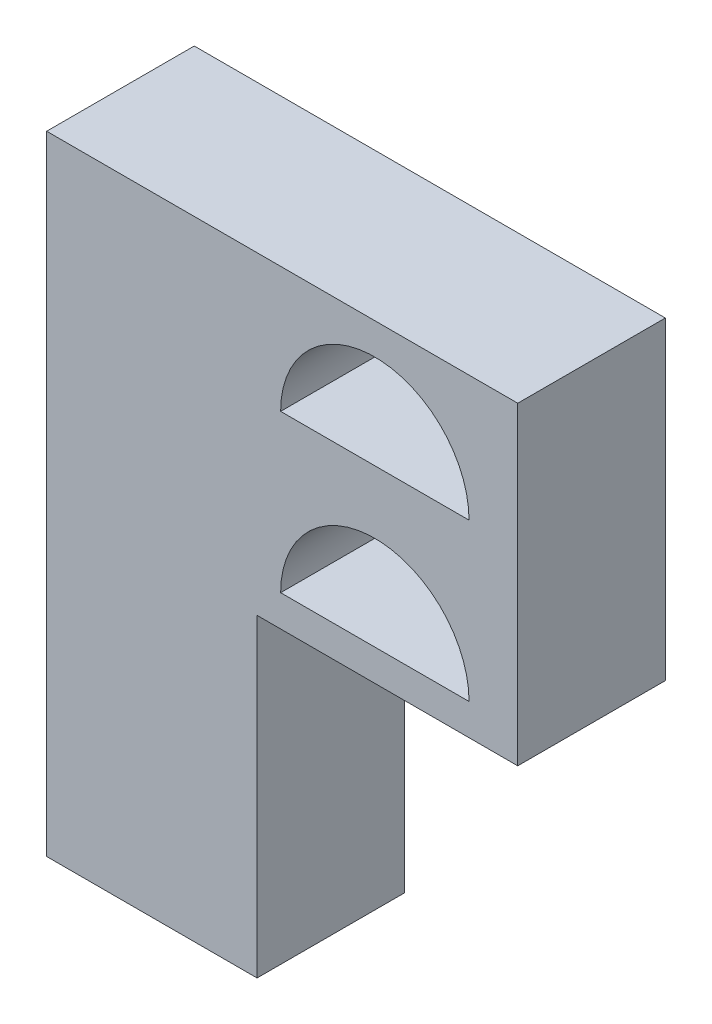
SolidWorks part; units mm, degrees
ref_plane "Front Plane" through (0, 0, 0) normal (0, 0, 1) x (1, 0, 0)
ref_plane "Top Plane" through (0, 0, 0) normal (0, 1, 0) x (1, 0, 0)
ref_plane "Right Plane" through (0, 0, 0) normal (1, 0, 0) x (0, 0, -1)
sketch "Sketch3" plane through (0, 0, 0) normal (0, 0, 1) x (1, 0, 0)
  line L0 (4.1, 15) -> (4.1, 0) construction
  line L2 (-3.35, 5) -> (-3.35, -5)
  line L3 (-3.35, -5) -> (3.35, -5)
  line L4 (3.35, 5) -> (3.35, -5)
  line L5 (-3.35, 5) -> (3.35, -5) construction
  line L6 (-3.35, -5) -> (3.35, 5) construction
  line L7 (3.35, 5) -> (6.63, 5)
  line L8 (-3.35, 5) -> (-3.35, 15)
  line L9 (-3.35, 15) -> (10.65, 15)
  line L11 (10.65, 10) -> (-3.35, 10) construction
  line L12 (10.1, 11) -> (4.1, 11) construction
  line L13 (6.63, 5) -> (3.35, 5)
  line L17 (6.63, 5) -> (10.65, 5)
  line L20 (10.1, 11) -> (4.1, 11)
  line L21 (10.65, 15) -> (11.65, 15)
  line L23 (10.1, 6) -> (4.1, 6)
  line L25 (10.65, 5) -> (11.65, 5)
  line L26 (11.65, 15) -> (11.65, 5)
  arc A1 (10.1, 11) -> (4.1, 11) centre (7.1, 11) ccw
  arc A2 (10.1, 6) -> (4.1, 6) centre (7.1, 6) ccw
  point P0 (0, 0)
  dimension "D1" = 6.7
  dimension "D2" = 10
  dimension "D3" = 1.5
  dimension "D4" = 1
  dimension "D5" = 14
  dimension "D6" = 1
  dimension "D7" = 2
  dimension "D8" = 6
extrude "Boss-Extrude2" add sketch "Sketch3" along normal blind 4.7
sketch "Sketch4" plane through (-3.35, 0, 0) normal (-1, 0, 0) x (0, 0, 1)
  line L0 (0, 5) -> (4.7, 5) construction
  line L1 (4.7, 15) -> (0, 15) construction
  line L6 (0, 10.0972) -> (4.7, 10.0972) construction
  line L10 (0, 12.5972) -> (4.7, 12.5972) construction
  line L11 (0.85, 9.3472) -> (3.85, 9.3472)
  line L12 (0, -5) -> (0, 15) construction
  line L13 (4.7, -5) -> (4.7, 15) construction
  line L14 (0.85, 14.3472) -> (3.85, 14.3472)
  line L15 (0.85, 14.3472) -> (0.85, 10.8472)
  line L16 (0.85, 10.8472) -> (3.85, 10.8472)
  line L17 (3.85, 14.3472) -> (3.85, 10.8472)
  line L18 (0.85, 14.3472) -> (3.85, 10.8472) construction
  line L19 (0.85, 10.8472) -> (3.85, 14.3472) construction
  line L20 (0.85, 5.8472) -> (0.85, 9.3472)
  line L21 (0.85, 5.8472) -> (3.85, 5.8472)
  line L22 (3.85, 5.8472) -> (3.85, 9.3472)
  point P1 (2.35, 10.0972)
  point P7 (2.35, 12.5972)
  dimension "D1" = 2.5
  dimension "D2" = 3.5
  dimension "D3" = 3
  dimension "D4" = 10
extrude "Cut-Extrude1" cut sketch "Sketch4" against normal blind 5
